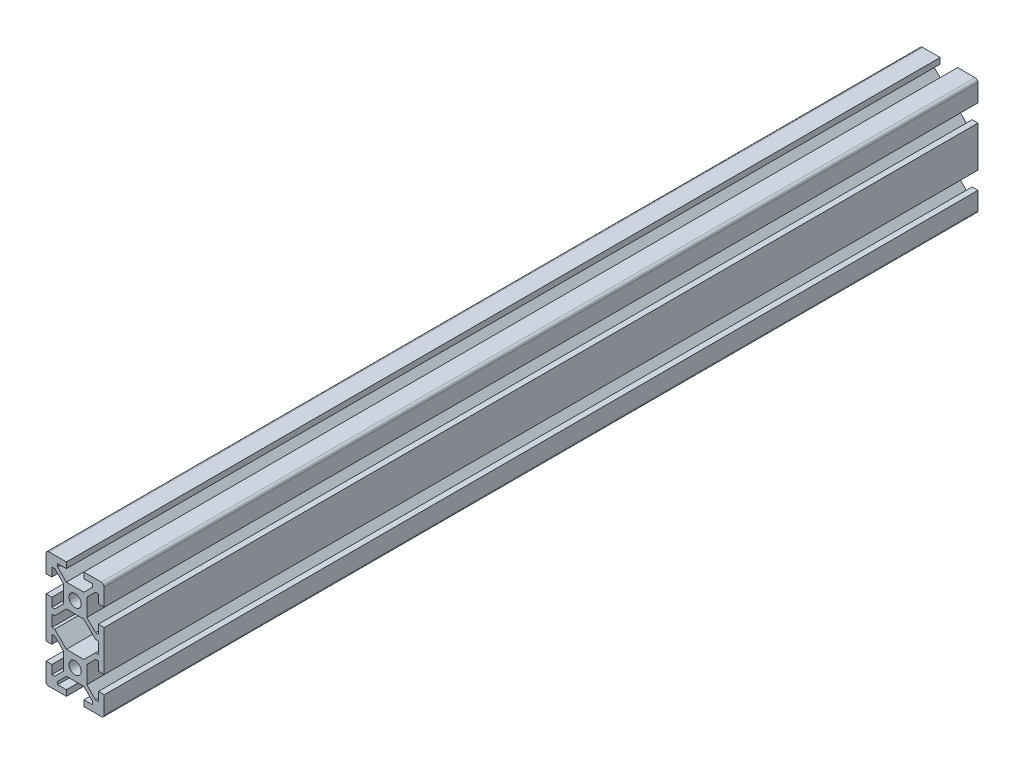
SolidWorks part; units mm, degrees
material "6063-O, Barra estrusa (SS)"
ref_plane "Piano frontale" through (0, 0, 0) normal (0, 0, 1) x (1, 0, 0)
ref_plane "Piano superiore" through (0, 0, 0) normal (0, 1, 0) x (1, 0, 0)
ref_plane "Piano destro" through (0, 0, 0) normal (1, 0, 0) x (0, 0, -1)
other "Lunghezza"
other "Lunghezze"
sketch "Schizzo1" plane through (0, 0, 0) normal (0, 0, 1) x (1, 0, 0)
  line L0 (-6, 18) -> (6, 18) construction
  line L1 (10, 20) -> (-10, 20) construction
  line L2 (10, 20) -> (10, -20) construction
  line L3 (-8, 4) -> (-8, -4) construction
  line L4 (-10, 20) -> (-10, -20) construction
  line L5 (10, 20) -> (-10, 0) construction
  line L6 (10, 0) -> (-10, 20) construction
  line L7 (-3, 14) -> (3, 14) construction
  line L8 (-3, 32.3825) -> (-3, 22.2883) construction
  line L9 (0, 33.8953) -> (0, -6.3729) construction
  line L10 (3, 32.3825) -> (3, 22.2883) construction
  line L11 (-6, 11.8152) -> (-6, 23.4013) construction
  line L12 (6, 10.4596) -> (6, 33.4013) construction
  line L13 (-3, 14) -> (-9, 20) construction
  line L14 (-10, 20) -> (-3, 20)
  line L15 (-3, 20) -> (-3, 18)
  line L16 (-3, 18) -> (-6, 18)
  line L17 (-6, 18) -> (-6, 17)
  line L18 (-6, 17) -> (-3, 14)
  line L19 (-3, 14) -> (3, 14)
  line L20 (3, 14) -> (9, 20) construction
  line L21 (3, 14) -> (6, 17)
  line L22 (6, 17) -> (6, 18)
  line L23 (6, 18) -> (3, 18)
  line L24 (3, 18) -> (3, 20)
  line L25 (3, 20) -> (10, 20)
  line L26 (10, 20) -> (10, 13)
  line L27 (10, 13) -> (8, 13)
  line L28 (8, 13) -> (8, 16)
  line L29 (8, 16) -> (7, 16)
  line L30 (7, 16) -> (4, 13)
  line L31 (4, 13) -> (4, 7)
  line L32 (4, 7) -> (7, 4)
  line L33 (8, 4) -> (8, 7)
  line L34 (7, 4) -> (8, 4)
  line L35 (8, 7) -> (10, 7)
  line L36 (10, 7) -> (10, 0)
  line L37 (8, 4) -> (8, -4) construction
  line L38 (-7, 4) -> (-7, -4) construction
  line L39 (7, 4) -> (7, -4) construction
  line L40 (3, -6) -> (7, -2)
  line L41 (-3, 6) -> (-7, 2)
  line L42 (3, 6) -> (-3, 6)
  line L43 (3, 6) -> (7, 2)
  line L44 (-3, -6) -> (-7, -2)
  line L45 (-7, -2) -> (-8, -2)
  line L46 (-8, -2) -> (-8, 2)
  line L47 (-8, 2) -> (-7, 2)
  line L48 (-10, 0) -> (-10, 7)
  line L49 (-10, 7) -> (-8, 7)
  line L50 (-8, 7) -> (-8, 4)
  line L51 (-8, 4) -> (-7, 4)
  line L52 (-7, 4) -> (-4, 7)
  line L53 (-4, 7) -> (-4, 13)
  line L54 (-4, 13) -> (-7, 16)
  line L55 (-8, 16) -> (-8, 13)
  line L56 (-7, 16) -> (-8, 16)
  line L57 (-8, 13) -> (-10, 13)
  line L58 (-10, 13) -> (-10, 20)
  line L59 (-19.9461, 0) -> (34.5024, 0) construction
  line L60 (3, -14) -> (9, -20) construction
  line L61 (-3, -14) -> (-9, -20) construction
  line L62 (-3, -14) -> (3, -14) construction
  line L63 (10, 0) -> (-10, -20) construction
  line L64 (10, -20) -> (-10, 0) construction
  line L65 (10, -20) -> (-10, -20) construction
  line L66 (-6, -18) -> (6, -18) construction
  line L67 (-10, -13) -> (-10, -20)
  line L68 (-8, -13) -> (-10, -13)
  line L69 (-7, -16) -> (-8, -16)
  line L70 (-8, -16) -> (-8, -13)
  line L71 (-4, -13) -> (-7, -16)
  line L72 (-4, -7) -> (-4, -13)
  line L73 (-7, -4) -> (-4, -7)
  line L74 (-8, -4) -> (-7, -4)
  line L75 (-8, -7) -> (-8, -4)
  line L76 (-10, -7) -> (-8, -7)
  line L77 (-10, 0) -> (-10, -7)
  line L78 (7, -2) -> (8, -2)
  line L79 (8, -2) -> (8, 2)
  line L80 (8, 2) -> (7, 2)
  line L81 (3, -6) -> (-3, -6)
  line L85 (10, -7) -> (10, 0)
  line L86 (8, -7) -> (10, -7)
  line L87 (7, -4) -> (8, -4)
  line L88 (8, -4) -> (8, -7)
  line L89 (4, -7) -> (7, -4)
  line L90 (4, -13) -> (4, -7)
  line L91 (7, -16) -> (4, -13)
  line L92 (8, -16) -> (7, -16)
  line L93 (8, -13) -> (8, -16)
  line L94 (10, -13) -> (8, -13)
  line L95 (10, -20) -> (10, -13)
  line L96 (3, -20) -> (10, -20)
  line L97 (3, -18) -> (3, -20)
  line L98 (6, -18) -> (3, -18)
  line L99 (6, -17) -> (6, -18)
  line L100 (3, -14) -> (6, -17)
  line L101 (-3, -14) -> (3, -14)
  line L102 (-6, -17) -> (-3, -14)
  line L103 (-6, -18) -> (-6, -17)
  line L104 (-3, -18) -> (-6, -18)
  line L105 (-3, -20) -> (-3, -18)
  line L106 (-10, -20) -> (-3, -20)
  line L107 (-3, 0) -> (-10, 0) [skipped]
  line L108 (-3, 0) -> (-3, -2) [skipped]
  line L109 (3, 0) -> (3, 2) [skipped]
  line L110 (10, 0) -> (3, 0) [skipped]
  line L111 (-6, 3) -> (-6, 2) [skipped]
  line L112 (-6, 2) -> (-3, 2) [skipped]
  line L113 (3, 2) -> (6, 2) [skipped]
  line L114 (6, 2) -> (6, 3) [skipped]
  line L115 (-3, 6) -> (-6, 3) [skipped]
  line L116 (6, 3) -> (3, 6) [skipped]
  circle A0 centre (0, 10) radius 2.1
  circle A1 centre (0, -10) radius 2.1
  point P0 (0, 10)
  point P5 (0, 14)
  point P11 (0, 18)
  point P71 (0, 10)
  dimension "D8" = 4.2
  dimension "D2" = 20
  dimension "D3" = 2
  dimension "D4" = 4
  dimension "D5" = 6
  dimension "D6" = 12
  dimension "D7" = 4
  dimension "D9" = 6
  dimension "D10" = 3
  dimension "D11" = 40
extrude "Estrusione-Estrusione1" add sketch "Schizzo1" along normal blind 300 contours L67 L106 L105 L104 L103 L102 L101 L100 L99 L98 L97 L96 L95 L94 L93 L92 L91 L90 L89 L87 L88 L86 L85 L36 L35 L33 L34 L32 L31 L30 L29 L28 L27 L26 L25 L24 L23 L22 L21 L19 L18 L17 L16 L15 L14 L58 L57 L55 L56 L54 L53
fillet "Raccordo1" radius 1 4 edges at (-10, -20, 150) (10, -20, 150) (-10, 20, 150) (10, 20, 150)
